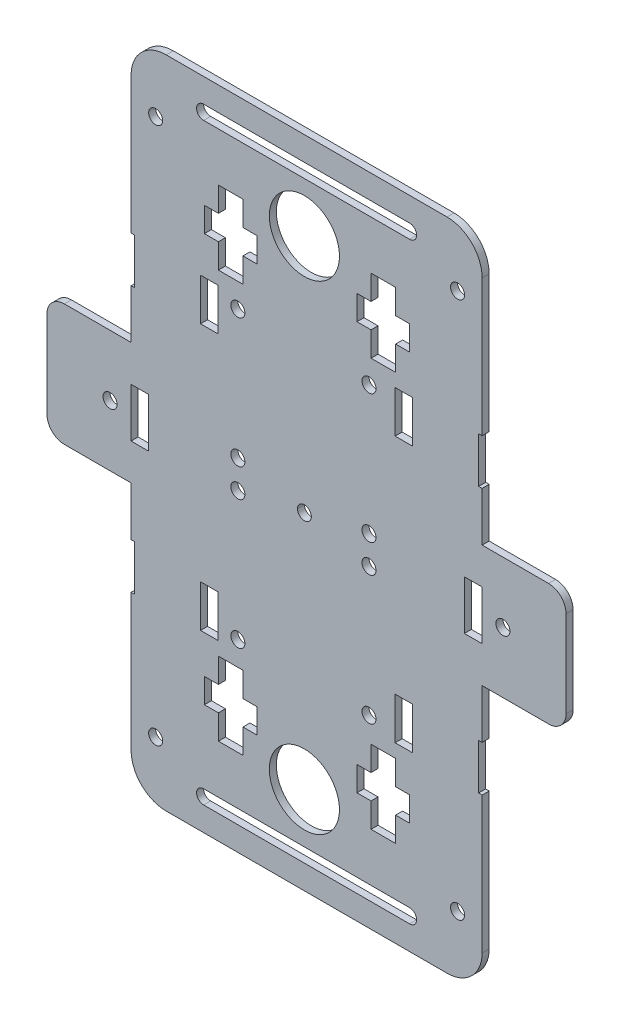
SolidWorks part; units mm, degrees
ref_plane "Front Plane" through (0, 0, 0) normal (0, 0, 1) x (1, 0, 0)
ref_plane "Top Plane" through (0, 0, 0) normal (0, 1, 0) x (1, 0, 0)
ref_plane "Right Plane" through (0, 0, 0) normal (1, 0, 0) x (0, 0, -1)
sketch "Sketch1" plane through (0, 0, 0) normal (0, 0, 1) x (1, 0, 0)
  line L0 (75, 4.4244) -> (-75, 4.4244) construction
  line L1 (0, 72.7324) -> (0, -63.8836) construction
  line L2 (-49.4, 97.7754) -> (-49.4, 48.7754)
  line L3 (-49.4, 21.7754) -> (-73.4, 21.7754)
  line L4 (-73.4, 21.7754) -> (-73.4, -12.9246)
  line L5 (-73.4, -12.9246) -> (-49.4, -12.9246)
  line L6 (-49.4, -12.9246) -> (-49.4, -26.9246)
  line L7 (50.6691, 97.7754) -> (-49.4, 97.7754) construction
  line L8 (50.6, -12.9246) -> (50.6, -26.9246)
  line L9 (50.6, -12.9246) -> (74.6, -12.9246)
  line L10 (74.6, -12.9246) -> (74.6, 21.7754)
  line L11 (74.6, 21.7754) -> (50.6691, 21.7754)
  line L12 (50.6691, 97.7754) -> (50.6691, 48.7754)
  line L13 (0, 72.7324) -> (0, 138.6441) construction
  line L14 (-73.4946, 97.7754) -> (-49.4, 97.7754)
  line L15 (50.6691, 97.7754) -> (74.6691, 97.7754)
  line L16 (-73.3495, -88.9246) -> (-49.4, -88.9246)
  line L17 (50.6, -88.9246) -> (74.5495, -88.9246)
  line L18 (-49.4, 48.7754) -> (-48.4, 48.7754)
  line L19 (-48.4, 48.7754) -> (-48.4, 35.7754)
  line L20 (-48.4, 35.7754) -> (-49.4, 35.7754)
  line L21 (-49.4, 35.7754) -> (-49.4, 21.7754)
  line L22 (50.6691, 48.7754) -> (49.6691, 48.7754)
  line L23 (49.6691, 48.7754) -> (49.6691, 35.7754)
  line L24 (49.6691, 35.7754) -> (50.6691, 35.7754)
  line L25 (50.6691, 35.7754) -> (50.6691, 21.7754)
  line L26 (-49.4, -26.9246) -> (-48.4, -26.9246)
  line L27 (-48.4, -39.9246) -> (-49.4, -39.9246)
  line L28 (-49.4, -39.9246) -> (-49.4, -88.9246)
  line L29 (-48.4, -26.9246) -> (-48.4, -39.9246)
  line L30 (-49.4, -88.9246) -> (50.6, -88.9246) construction
  line L31 (50.6, -26.9246) -> (49.6, -26.9246)
  line L32 (49.6, -26.9246) -> (49.6, -39.9246)
  line L33 (49.6, -39.9246) -> (50.6, -39.9246)
  line L34 (50.6, -39.9246) -> (50.6, -88.9246)
  line L36 (-48.4, 33.9331) -> (-48.4, 66.1831) construction
  circle A2 centre (0, 72.7324) radius 10
  circle A3 centre (0, -63.8836) radius 10
  circle A4 centre (0, 4.4244) radius 1.9726
  ellipse E0 centre (0.5873, 97.7754) end of major axis (-73.4946, 97.7754) minor radius 35 (-73.4946, 97.7754) -> (74.6691, 97.7754) cw
  ellipse E1 centre (0.6, -88.9246) end of major axis (74.6, -90.6246) minor radius 34.5333 (-73.3495, -88.9246) -> (74.5495, -88.9246) ccw
  point P4 (0, 4.4244)
  point P8 (0, 4.4244)
  point P39 (-0.1931, -123.4488)
  point P53 (-49.4, 97.7754)
  dimension "D11" = 13
  dimension "D12" = 49
  dimension "D13" = 34.7
  dimension "D1" = 49
  dimension "D9" = 49
  dimension "D10" = 14
  dimension "D2" = 13
  dimension "D3" = 14
  dimension "D4" = 14
  dimension "D5" = 13
  dimension "D6" = 49
  dimension "D7" = 14
  dimension "D8" = 13
  dimension "D14" = 34.7
  dimension "D15" = 1
  dimension "D16" = 1
  dimension "D17" = 1
  dimension "D18" = 1
  dimension "D19" = 1
  dimension "D20" = 1
  dimension "D21" = 1
  dimension "D22" = 1
  dimension "D23" = 23.9495
  dimension "D24" = 23.9495
  dimension "D25" = 24
  dimension "D26" = 24.0946
  dimension "D27" = 24
  dimension "D28" = 23.9309
  dimension "D29" = 24
  dimension "D30" = 24
extrude "Boss-Extrude2" add sketch "Sketch1" along normal blind 2
sketch "Sketch5" plane through (0, 0, 0) normal (0, 0, -1) x (-1, 0, 0)
  line L0 (49.4, 21.7754) -> (73.4, 21.7754) construction
  line L1 (44.4, 11.4254) -> (49.4, 11.4254)
  line L2 (44.4, 11.4254) -> (44.4, -2.5746)
  line L3 (44.4, -2.5746) -> (49.4, -2.5746)
  line L4 (49.4, 11.4254) -> (49.4, -2.5746)
  line L5 (73.4, 21.7754) -> (73.4, -12.9246) construction
  dimension "D1" = 5
  dimension "D2" = 14
  dimension "D3" = 10.35
  dimension "D4" = 10.35
  dimension "D5" = 29
extrude "Cut-Extrude3" cut sketch "Sketch5" against normal through all
sketch "Sketch6" plane through (0, 0, 0) normal (0, 0, -1) x (-1, 0, 0)
  line L0 (-74.6, -12.9246) -> (-74.6, 21.7754) construction
  line L1 (-50.6, 11.4254) -> (-45.6, 11.4254)
  line L2 (-50.6, 11.4254) -> (-50.6, -2.5746)
  line L3 (-50.6, -2.5746) -> (-45.6, -2.5746)
  line L4 (-45.6, 11.4254) -> (-45.6, -2.5746)
  line L5 (-50.6, -12.9246) -> (-74.6, -12.9246) construction
  line L6 (-74.6, 21.7754) -> (-50.6691, 21.7754) construction
  dimension "D1" = 5
  dimension "D2" = 14
  dimension "D3" = 29
  dimension "D4" = 10.35
  dimension "D5" = 10.35
extrude "Cut-Extrude4" cut sketch "Sketch6" against normal through all
sketch "Sketch19" plane through (0, 0, 0) normal (0, 0, -1) x (-1, 0, 0)
  line L1 (-50.6, 11.4254) -> (-50.6, -2.5746) construction
  circle A0 centre (-56.6, 4.4254) radius 2
  point P3 (-56.6, 4.4254)
  point P4 (-50.6, 4.4254)
extrude "Cut-Extrude19" cut sketch "Sketch19" against normal through all
sketch "Sketch22" plane through (0, 0, 0) normal (0, 0, -1) x (-1, 0, 0)
  line L1 (49.4, 97.7754) -> (49.4, 48.7754) construction
  line L2 (-50.6691, 48.7754) -> (-50.6691, 97.7754) construction
  circle A0 centre (42.4, 81) radius 2
  circle A1 centre (-43.6691, 81) radius 2
  point P5 (4, 81)
  dimension "D1" = 4
  dimension "D3" = 4
  dimension "D2" = 7
  dimension "D4" = 7
extrude "Cut-Extrude22" cut sketch "Sketch22" against normal through all
sketch "Sketch23" plane through (0, 0, 2) normal (0, 0, 1) x (1, 0, 0)
  line L0 (-49.4, -39.9246) -> (-49.4, -88.9246) construction
  line L2 (50.6, -88.9246) -> (50.6, -39.9246) construction
  circle A0 centre (43.6, -81) radius 2
  circle A1 centre (-42.4, -81) radius 2
  point P4 (0.6147, -81)
  point P10 (0.6147, -81)
  dimension "D1" = 4
  dimension "D3" = 4
  dimension "D2" = 7
  dimension "D4" = 7
extrude "Cut-Extrude23" cut sketch "Sketch23" against normal through all
sketch "Sketch24" plane through (0, 0, 2) normal (0, 0, 1) x (1, 0, 0)
  line L0 (50.6691, 97.7754) -> (74.6691, 97.7754) construction
  line L1 (-73.4946, 97.7754) -> (-49.4, 97.7754) construction
  line L2 (74.5495, -88.9246) -> (50.6, -88.9246) construction
  line L3 (-49.4, -88.9246) -> (-73.3495, -88.9246) construction
  circle A0 centre (-50, -94.9246) radius 2
  circle A1 centre (50, -94.9246) radius 2
  circle A2 centre (-50, 103.7754) radius 2
  circle A3 centre (50, 103.7754) radius 2
  dimension "D1" = 4
  dimension "D3" = 4
  dimension "D9" = 4
  dimension "D10" = 4
  dimension "D11" = 6
  dimension "D12" = 6
  dimension "D13" = 6
  dimension "D14" = 6
extrude "Cut-Extrude24" cut sketch "Sketch24" against normal through all
sketch "Sketch25" plane through (0, 0, 0) normal (0, 0, -1) x (-1, 0, 0)
  line L1 (-30.8691, 48.2754) -> (-30.8691, 34.1932) construction
  line L5 (-30.8691, 48.2754) -> (-25.8691, 48.2754)
  line L6 (-30.8691, 48.2754) -> (-30.8691, 36.2754)
  line L7 (-30.8691, 36.2754) -> (-25.8691, 36.2754)
  line L8 (-25.8691, 48.2754) -> (-25.8691, 36.2754)
  line L12 (24.6, 48.2754) -> (29.6, 48.2754)
  line L13 (24.6, 48.2754) -> (24.6, 36.2754)
  line L14 (24.6, 36.2754) -> (29.6, 36.2754)
  line L15 (29.6, 48.2754) -> (29.6, 36.2754)
  line L22 (-30.8, -27.4246) -> (-25.8, -27.4246)
  line L23 (-30.8, -27.4246) -> (-30.8, -39.4246)
  line L24 (-30.8, -39.4246) -> (-25.8, -39.4246)
  line L25 (-25.8, -27.4246) -> (-25.8, -39.4246)
  line L26 (24.6, -27.4246) -> (29.6, -27.4246)
  line L27 (24.6, -27.4246) -> (24.6, -39.4246)
  line L28 (24.6, -39.4246) -> (29.6, -39.4246)
  line L29 (29.6, -27.4246) -> (29.6, -39.4246)
  dimension "D1" = 12
  dimension "D2" = 5
  dimension "D3" = 12
  dimension "D4" = 12
  dimension "D5" = 5
  dimension "D6" = 12
  dimension "D7" = 5
  dimension "D8" = 5
extrude "Cut-Extrude25" cut sketch "Sketch25" against normal through all
sketch "Sketch29" plane through (0, 0, 0) normal (0, 0, -1) x (-1, 0, 0)
  line L4 (-30.291, -39.4246) -> (-30.291, -50.2246) construction
  line L5 (-30.8, -39.4246) -> (-25.8, -39.4246) construction
  line L6 (29.1154, -39.4246) -> (29.1154, -50.2246) construction
  line L7 (24.6, -39.4246) -> (29.6, -39.4246) construction
sketch "Sketch26" plane through (0, 0, 0) normal (0, 0, -1) x (-1, 0, 0)
  line L0 (24.5102, 52.0754) -> (17.5102, 52.0754)
  line L1 (24.5102, 52.0754) -> (24.5102, 59.0754) construction
  line L2 (-25.9991, 73.0754) -> (-18.9991, 73.0754) construction
  line L3 (17.5102, 52.0754) -> (17.5102, 59.0754)
  line L4 (17.5102, 59.0754) -> (13.5102, 59.0754)
  line L5 (-29.9991, 59.0754) -> (-29.9991, 66.0754)
  line L6 (13.5102, 59.0754) -> (13.5102, 66.0754)
  line L7 (-14.9991, 66.0754) -> (-14.9991, 59.0754)
  line L8 (13.5102, 66.0754) -> (17.5102, 66.0754)
  line L9 (-25.9991, 52.0754) -> (-18.9991, 52.0754)
  line L10 (-18.9991, 52.0754) -> (-18.9991, 59.0754)
  line L11 (-18.9991, 59.0754) -> (-14.9991, 59.0754)
  line L12 (-14.9991, 66.0754) -> (-18.9991, 66.0754)
  line L13 (-18.9991, 66.0754) -> (-18.9991, 73.0754)
  line L14 (-18.9991, 73.0754) -> (-25.9991, 73.0754)
  line L15 (-25.9991, 73.0754) -> (-25.9991, 66.0754)
  line L16 (-25.9991, 66.0754) -> (-29.9991, 66.0754)
  line L17 (-29.9991, 59.0754) -> (-25.9991, 59.0754)
  line L18 (-25.9991, 59.0754) -> (-25.9991, 52.0754)
  line L19 (17.5102, 66.0754) -> (17.5102, 73.0754)
  line L20 (17.5102, 73.0754) -> (24.5102, 73.0754)
  line L21 (24.5102, 73.0754) -> (24.5102, 66.0754)
  line L22 (24.5102, 66.0754) -> (28.5102, 66.0754)
  line L23 (28.5102, 66.0754) -> (28.5102, 59.0754)
  line L24 (28.5102, 59.0754) -> (24.5102, 59.0754)
  line L27 (29.1154, -39.4246) -> (29.1154, -50.2246) construction
  line L28 (-30.291, -39.4246) -> (-30.291, -50.2246) construction
  line L35 (24.5102, 59.0754) -> (24.5102, 52.0754)
  line L36 (-19, -69) -> (-19, -62)
  line L37 (-26, -48) -> (-19, -48)
  line L38 (-19, -48) -> (-19, -55)
  line L39 (-19, -55) -> (-15, -55)
  line L40 (-15, -55) -> (-15, -62)
  line L41 (-15, -62) -> (-19, -62)
  line L42 (-19, -69) -> (-26, -69)
  line L43 (-26, -69) -> (-26, -62)
  line L44 (-26, -62) -> (-30, -62)
  line L45 (-30, -62) -> (-30, -55)
  line L46 (-30, -55) -> (-26, -55)
  line L47 (-26, -55) -> (-26, -48)
  line L49 (24.5102, -48) -> (17.5102, -48)
  line L50 (17.5102, -48) -> (17.5102, -55)
  line L51 (17.5102, -55) -> (13.5102, -55)
  line L52 (13.5102, -55) -> (13.5102, -62)
  line L53 (13.5102, -62) -> (17.5102, -62)
  line L54 (17.5102, -62) -> (17.5102, -69)
  line L55 (17.5102, -69) -> (24.5102, -69)
  line L56 (24.5102, -69) -> (24.5102, -62)
  line L57 (24.5102, -62) -> (28.5102, -62)
  line L58 (28.5102, -62) -> (28.5102, -55)
  line L59 (28.5102, -55) -> (24.5102, -55)
  line L60 (24.5102, -55) -> (24.5102, -48)
  point P26 (-26, -48)
  dimension "D1" = 15
  dimension "D2" = 21
  dimension "D3" = 7
  dimension "D4" = 7
  dimension "D5" = 4
  dimension "D6" = 7
  dimension "D7" = 7
  dimension "D8" = 7
  dimension "D9" = 15
  dimension "D10" = 21
  dimension "D11" = 7
  dimension "D12" = 7
  dimension "D13" = 4
  dimension "D14" = 4
  dimension "D15" = 4
  dimension "D16" = 4
  dimension "D17" = 7
  dimension "D18" = 7
extrude "Cut-Extrude26" cut sketch "Sketch26" against normal through all
sketch "Sketch28" plane through (0, 0, 0) normal (0, 0, -1) x (-1, 0, 0)
  line L0 (-50.6691, 97.7754) -> (49.4, 97.7754) construction
  line L1 (30, -112) -> (-30, -112)
  line L2 (-30, 118.8223) -> (30, 118.8223) construction
  line L3 (-30, 120.8223) -> (30, 120.8223)
  line L4 (-30, 116.8223) -> (30, 116.8223)
  line L5 (-30, -112) -> (30, -112) construction
  line L6 (-30, -110) -> (30, -110)
  line L7 (-30, -114) -> (30, -114)
  line L8 (-65.7732, 104.3331) -> (-40.7732, 117.3331) construction
  line L9 (-66.6959, 106.1075) -> (-41.6959, 119.1075)
  line L10 (-64.8505, 102.5586) -> (-39.8505, 115.5586)
  line L11 (38.5049, 117.1628) -> (65.4902, 104.1735) construction
  line L12 (39.3724, 118.9649) -> (66.3577, 105.9756)
  line L13 (37.6375, 115.3607) -> (64.6228, 102.3714)
  line L14 (-50.6691, 88.9285) -> (49.4, 88.9285) construction
  line L15 (-50.6691, 48.7754) -> (-50.6691, 97.7754) construction
  line L16 (49.4, 97.7754) -> (49.4, 48.7754) construction
  line L17 (28.7309, 88.9285) -> (-30, 88.9285) construction
  line L18 (28.7309, 86.9285) -> (-30, 86.9285)
  line L19 (28.7309, 90.9285) -> (-30, 90.9285)
  line L21 (36, -112) -> (63, -99) construction
  line L22 (35.1324, -110.198) -> (62.1324, -97.198)
  line L23 (36.8676, -113.802) -> (63.8676, -100.802)
  line L24 (-63, -99) -> (-38, -112.1208) construction
  line L25 (-62.0706, -97.2291) -> (-37.0706, -110.3499)
  line L26 (-63.9294, -100.7709) -> (-38.9294, -113.8918)
  arc A0 (-30, 120.8223) -> (-30, 116.8223) centre (-30, 118.8223) ccw
  arc A1 (30, 116.8223) -> (30, 120.8223) centre (30, 118.8223) ccw
  arc A2 (-66.6959, 106.1075) -> (-64.8505, 102.5586) centre (-65.7732, 104.3331) ccw
  arc A3 (28.7309, 86.9285) -> (28.7309, 90.9285) centre (28.7309, 88.9285) ccw
  arc A4 (-39.8505, 115.5586) -> (-41.6959, 119.1075) centre (-40.7732, 117.3331) ccw
  arc A5 (39.3724, 118.9649) -> (37.6375, 115.3607) centre (38.5049, 117.1628) ccw
  arc A6 (64.6228, 102.3714) -> (66.3577, 105.9756) centre (65.4902, 104.1735) ccw
  arc A7 (35.1324, -110.198) -> (36.8676, -113.802) centre (36, -112) ccw
  arc A8 (-30, -110) -> (-30, -114) centre (-30, -112) ccw
  arc A9 (30, -114) -> (30, -110) centre (30, -112) ccw
  arc A10 (-30, 90.9285) -> (-30, 86.9285) centre (-30, 88.9285) ccw
  arc A11 (63.8676, -100.802) -> (62.1324, -97.198) centre (63, -99) ccw
  arc A12 (-62.0706, -97.2291) -> (-63.9294, -100.7709) centre (-63, -99) ccw
  arc A13 (-38.9294, -113.8918) -> (-37.0706, -110.3499) centre (-38, -112.1208) ccw
  point P4 (0, -112)
  point P6 (0, -112)
  point P10 (0, 118.8223)
  point P15 (-36, -112)
  point P16 (0, -112)
  point P22 (-30, -112)
  point P23 (-38, -112.1208)
  point P25 (65.4902, 104.1735)
  point P26 (-40.7732, 117.3331)
  point P29 (-53.2732, 110.8331)
  point P35 (34, -112)
  point P36 (38.5049, 117.1628)
  point P39 (51.9976, 110.6681)
  point P44 (30, -112)
  point P49 (-0.6346, 88.9285)
  point P57 (36, -112)
  point P60 (49.5, -105.5)
  point P65 (-50.5, -105.5604)
  dimension "D1" = 4
extrude "Cut-Extrude29" cut sketch "Sketch28" against normal through all contours L18 A10 L19 A3
sketch "Sketch20" plane through (0, 0, 0) normal (0, 0, -1) x (-1, 0, 0)
  circle A1 centre (55.4, 4.4254) radius 2
  dimension "D1" = 4
extrude "Cut-Extrude20" cut sketch "Sketch20" against normal through all
sketch "Sketch30" plane through (0, 0, 0) normal (0, 0, -1) x (-1, 0, 0)
  line L3 (-93.3825, 4.4254) -> (88.3139, 4.4254)
  line L4 (-93.3825, 4.4254) -> (-93.3825, -127.0315)
  line L5 (-93.3825, -127.0315) -> (88.3139, -127.0315)
  line L6 (88.3139, 4.4254) -> (88.3139, -127.0315)
extrude "Cut-Extrude30" cut sketch "Sketch30" against normal blind 3 contours L4 L3 L6 L5
ref_plane "Plane1" through (0, 4.4254, 0) normal (0, -1, 0) x (-1, 0, 0)
sketch "Sketch31" plane through (0, 0, 0) normal (0, 0, -1) x (-1, 0, 0)
  line L0 (21.7811, 5.0804) -> (-21.4189, 5.0804) construction
  line L1 (21.7811, 5.0804) -> (21.7811, 48.2804) construction
  line L2 (21.7811, 48.2804) -> (-21.4189, 48.2804) construction
  line L3 (-21.4189, 5.0804) -> (-21.4189, 48.2804) construction
  circle A0 centre (-18.413, 45.2129) radius 2
  circle A1 centre (-18.4137, 8.4729) radius 2
  circle A2 centre (18.967, 45.2129) radius 2
  circle A3 centre (18.9663, 8.4729) radius 2
  point P2 (0.1811, 26.6804)
  dimension "D1" = 43.2
  dimension "D2" = 43.2
  dimension "D3" = 36.74
  dimension "D4" = 37.38
  dimension "D5" = 36.74
  dimension "D6" = 37.38
  dimension "D7" = 52.4122
  dimension "D8" = 52.4132
extrude "Cut-Extrude31" cut sketch "Sketch31" against normal blind 2
sketch "Sketch32" plane through (0, 0, 0) normal (0, 0, -1) x (-1, 0, 0)
  line L1 (79.0694, 97.7754) -> (-88.3924, 97.7754)
  line L2 (79.0694, 97.7754) -> (79.0694, 135.0434)
  line L3 (79.0694, 135.0434) -> (-88.3924, 135.0434)
  line L4 (-88.3924, 97.7754) -> (-88.3924, 135.0434)
extrude "Cut-Extrude32" cut sketch "Sketch32" against normal blind 2
fillet "Fillet1" radius 10 2 edges at (-49.4, 97.7754, 1) (50.6691, 97.7754, 1)
fillet "Fillet2" radius 5 2 edges at (-73.4, 21.7754, 1) (74.6, 21.7754, 1)
mirror "Mirror1" about plane through (0, 4.4254, 0) normal (0, -1, 0) of bodies 143
